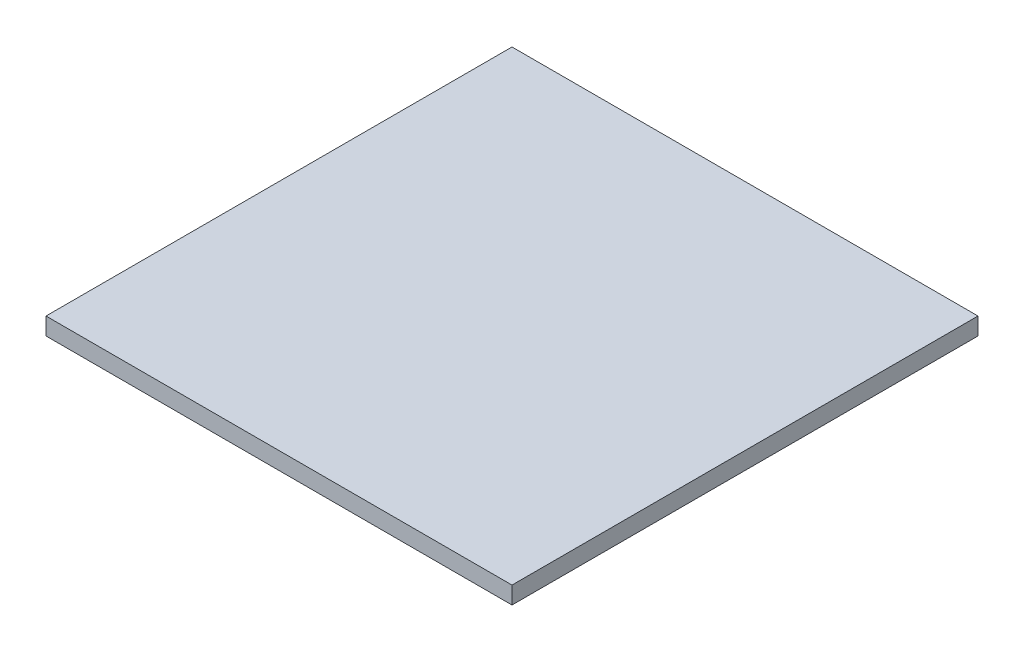
SolidWorks part; units mm, degrees
material "Plastique personnalisé"
ref_plane "Plan de face" through (0, 0, 0) normal (0, 0, 1) x (1, 0, 0)
ref_plane "Plan de dessus" through (0, 0, 0) normal (0, 1, 0) x (1, 0, 0)
ref_plane "Plan de droite" through (0, 0, 0) normal (1, 0, 0) x (0, 0, -1)
sketch "Esquisse1" plane through (0, 0, 0) normal (0, 1, 0) x (1, 0, 0)
  line L1 (0, 0) -> (7, 0)
  line L2 (0, 0) -> (0, 7)
  line L3 (0, 7) -> (7, 7)
  line L4 (7, 0) -> (7, 7)
  dimension "D1" = 7
  dimension "D2" = 7
extrude "Boss.-Extru.1" add sketch "Esquisse1" along normal blind 0.26
sketch "Esquisse2" plane through (0, 0, 0) normal (0, -1, 0) x (1, 0, 0)
  line L0 (7, -7) -> (6.2, -7) construction
  line L1 (7, -7) -> (0, -7) construction
  line L2 (7, -7) -> (7, -6.2) construction
  line L3 (7, 0) -> (7, -7) construction
  line L4 (0, 0) -> (0, -0.8) construction
  line L5 (0, -7) -> (0, 0) construction
  line L6 (0, 0) -> (0.8, 0) construction
  line L7 (0, 0) -> (7, 0) construction
  line L9 (6.2, -6.2) -> (0.8, -6.2)
  line L10 (6.2, -6.2) -> (6.2, -0.8)
  line L11 (6.2, -0.8) -> (0.8, -0.8)
  line L12 (0.8, -6.2) -> (0.8, -0.8)
  dimension "D1" = 0.8
  dimension "D2" = 0.8
  dimension "D3" = 0.8
  dimension "D4" = 0.8
extrude "Boss.-Extru.2" add sketch "Esquisse2" along normal blind 0.01
sketch "Esquisse5" plane through (0, 0, 0) normal (0, -1, 0) x (1, 0, 0)
  line L0 (7, 0) -> (7, -0.075) construction
  line L1 (7, 0) -> (7, -7) construction
  line L2 (7, -0.075) -> (0, -0.075) construction
  line L3 (0, -7) -> (0, 0) construction
  line L4 (0, 0) -> (0.075, 0) construction
  line L5 (0, 0) -> (7, 0) construction
  line L6 (0.075, 0) -> (0.075, -7) construction
  line L7 (7, -7) -> (0, -7) construction
  line L8 (0, -7) -> (0, -6.925) construction
  line L9 (0, -6.925) -> (7, -6.925) construction
  line L10 (7, -7) -> (6.925, -7) construction
  line L11 (6.925, -7) -> (6.925, 0) construction
  line L12 (6.2, -0.8) -> (6.2, 0) construction
  line L13 (6.2, -6.2) -> (6.2, -7) construction
  line L14 (6.2, -6.2) -> (7, -6.2) construction
  line L15 (6.2, -0.8) -> (7, -0.8) construction
  line L16 (0.8, -6.2) -> (0.8, -7) construction
  line L17 (0.8, -6.2) -> (0, -6.2) construction
  line L18 (0.8, -0.8) -> (0, -0.8) construction
  line L19 (0.8, -0.8) -> (0.8, 0) construction
  line L20 (0.075, -5.9312) -> (0.475, -5.9312)
  line L21 (0.075, -6.1812) -> (0.475, -6.1812)
  line L22 (0.075, -6.1812) -> (0.075, -6.4312)
  line L23 (0.075, -6.4312) -> (0.475, -6.4312)
  line L24 (0.475, -6.1812) -> (0.475, -6.4312)
  line L25 (0.475, -5.6812) -> (0.475, -5.9312)
  line L26 (0.075, -5.6812) -> (0.475, -5.6812)
  line L27 (0.075, -5.6812) -> (0.075, -5.9312)
  line L28 (0.075, 0.5) -> (0.075, -6.5) construction
  line L29 (0.075, -5.4312) -> (0.475, -5.4312)
  line L30 (0.475, -5.1812) -> (0.475, -5.4312)
  line L31 (0.075, -5.1812) -> (0.475, -5.1812)
  line L32 (0.075, -5.1812) -> (0.075, -5.4312)
  line L33 (0.075, 1) -> (0.075, -6) construction
  line L34 (0.075, -4.9312) -> (0.475, -4.9312)
  line L35 (0.475, -4.6812) -> (0.475, -4.9312)
  line L36 (0.075, -4.6812) -> (0.475, -4.6812)
  line L37 (0.075, -4.6812) -> (0.075, -4.9312)
  line L38 (0.075, 1.5) -> (0.075, -5.5) construction
  line L39 (0.075, -4.4312) -> (0.475, -4.4312)
  line L40 (0.475, -4.1812) -> (0.475, -4.4312)
  line L41 (0.075, -4.1812) -> (0.475, -4.1812)
  line L42 (0.075, -4.1812) -> (0.075, -4.4312)
  line L43 (0.075, 2) -> (0.075, -5) construction
  line L44 (0.075, -3.9312) -> (0.475, -3.9312)
  line L45 (0.475, -3.6812) -> (0.475, -3.9312)
  line L46 (0.075, -3.6812) -> (0.475, -3.6812)
  line L47 (0.075, -3.6812) -> (0.075, -3.9312)
  line L48 (0.075, 2.5) -> (0.075, -4.5) construction
  line L49 (0.075, -3.4312) -> (0.475, -3.4312)
  line L50 (0.475, -3.1812) -> (0.475, -3.4312)
  line L51 (0.075, -3.1812) -> (0.475, -3.1812)
  line L52 (0.075, -3.1812) -> (0.075, -3.4312)
  line L53 (0.075, 3) -> (0.075, -4) construction
  line L54 (0.075, -2.9312) -> (0.475, -2.9312)
  line L55 (0.475, -2.6812) -> (0.475, -2.9312)
  line L56 (0.075, -2.6812) -> (0.475, -2.6812)
  line L57 (0.075, -2.6812) -> (0.075, -2.9312)
  line L58 (0.075, 3.5) -> (0.075, -3.5) construction
  line L59 (0.075, -2.4312) -> (0.475, -2.4312)
  line L60 (0.475, -2.1812) -> (0.475, -2.4312)
  line L61 (0.075, -2.1812) -> (0.475, -2.1812)
  line L62 (0.075, -2.1812) -> (0.075, -2.4312)
  line L63 (0.075, 4) -> (0.075, -3) construction
  line L64 (0.075, -1.9312) -> (0.475, -1.9312)
  line L65 (0.475, -1.6812) -> (0.475, -1.9312)
  line L66 (0.075, -1.6812) -> (0.475, -1.6812)
  line L67 (0.075, -1.6812) -> (0.075, -1.9312)
  line L68 (0.075, 4.5) -> (0.075, -2.5) construction
  line L69 (0.075, -1.4312) -> (0.475, -1.4312)
  line L70 (0.475, -1.1812) -> (0.475, -1.4312)
  line L71 (0.075, -1.1812) -> (0.475, -1.1812)
  line L72 (0.075, -1.1812) -> (0.075, -1.4312)
  line L73 (0.075, 5) -> (0.075, -2) construction
  line L74 (0.075, -0.9312) -> (0.475, -0.9312)
  line L75 (0.475, -0.6812) -> (0.475, -0.9312)
  line L76 (0.075, -0.6812) -> (0.475, -0.6812)
  line L77 (0.075, -0.6812) -> (0.075, -0.9312)
  line L78 (0.075, 5.5) -> (0.075, -1.5) construction
  line L79 (3.5, -6.925) -> (3.5, -0.075) construction
  line L80 (6.925, -0.6812) -> (6.925, -0.9312)
  line L81 (6.925, -0.6812) -> (6.525, -0.6812)
  line L82 (6.525, -0.6812) -> (6.525, -0.9312)
  line L83 (6.925, -0.9312) -> (6.525, -0.9312)
  line L84 (6.925, -1.1812) -> (6.925, -1.4312)
  line L85 (6.925, -1.1812) -> (6.525, -1.1812)
  line L86 (6.525, -1.1812) -> (6.525, -1.4312)
  line L87 (6.925, -1.4312) -> (6.525, -1.4312)
  line L88 (6.925, -1.6812) -> (6.925, -1.9312)
  line L89 (6.925, -1.6812) -> (6.525, -1.6812)
  line L90 (6.525, -1.6812) -> (6.525, -1.9312)
  line L91 (6.925, -1.9312) -> (6.525, -1.9312)
  line L92 (6.925, -2.1812) -> (6.925, -2.4312)
  line L93 (6.925, -2.1812) -> (6.525, -2.1812)
  line L94 (6.525, -2.1812) -> (6.525, -2.4312)
  line L95 (6.925, -2.4312) -> (6.525, -2.4312)
  line L96 (6.925, -2.6812) -> (6.925, -2.9312)
  line L97 (6.925, -2.6812) -> (6.525, -2.6812)
  line L98 (6.525, -2.6812) -> (6.525, -2.9312)
  line L99 (6.925, -2.9312) -> (6.525, -2.9312)
  line L100 (6.925, -3.1812) -> (6.925, -3.4312)
  line L101 (6.925, -3.1812) -> (6.525, -3.1812)
  line L102 (6.525, -3.1812) -> (6.525, -3.4312)
  line L103 (6.925, -3.4312) -> (6.525, -3.4312)
  line L104 (6.925, -3.6812) -> (6.925, -3.9312)
  line L105 (6.925, -3.6812) -> (6.525, -3.6812)
  line L106 (6.525, -3.6812) -> (6.525, -3.9312)
  line L107 (6.925, -3.9312) -> (6.525, -3.9312)
  line L108 (6.925, -4.1812) -> (6.925, -4.4312)
  line L109 (6.925, -4.1812) -> (6.525, -4.1812)
  line L110 (6.525, -4.1812) -> (6.525, -4.4312)
  line L111 (6.925, -4.4312) -> (6.525, -4.4312)
  line L112 (6.925, -4.6812) -> (6.925, -4.9312)
  line L113 (6.925, -4.6812) -> (6.525, -4.6812)
  line L114 (6.525, -4.6812) -> (6.525, -4.9312)
  line L115 (6.925, -4.9312) -> (6.525, -4.9312)
  line L116 (6.925, -5.1812) -> (6.925, -5.4312)
  line L117 (6.925, -5.1812) -> (6.525, -5.1812)
  line L118 (6.525, -5.1812) -> (6.525, -5.4312)
  line L119 (6.925, -5.4312) -> (6.525, -5.4312)
  line L120 (6.925, -5.6812) -> (6.925, -5.9312)
  line L121 (6.925, -5.6812) -> (6.525, -5.6812)
  line L122 (6.525, -5.6812) -> (6.525, -5.9312)
  line L123 (6.925, -5.9312) -> (6.525, -5.9312)
  line L124 (6.925, -6.1812) -> (6.925, -6.4312)
  line L125 (6.925, -6.1812) -> (6.525, -6.1812)
  line L126 (6.525, -6.1812) -> (6.525, -6.4312)
  line L127 (6.925, -6.4312) -> (6.525, -6.4312)
  dimension "D1" = 0.25
  dimension "D2" = 0.4
  dimension "D3" = 12
extrude "Boss.-Extru.5" add sketch "Esquisse5" along normal blind 0.01
sketch "Esquisse6" plane through (0, 0, 0) normal (0, -1, 0) x (1, 0, 0)
  line L0 (5.6487, -6.9245) -> (5.8987, -6.9245)
  line L1 (6.1487, -6.9245) -> (6.3987, -6.9245)
  line L2 (6.1487, -6.9245) -> (6.1487, -6.5245)
  line L3 (6.1487, -6.5245) -> (6.3987, -6.5245)
  line L4 (6.3987, -6.9245) -> (6.3987, -6.5245)
  line L5 (5.8987, -6.9245) -> (5.8987, -6.5245)
  line L6 (5.6487, -6.5245) -> (5.8987, -6.5245)
  line L7 (5.6487, -6.9245) -> (5.6487, -6.5245)
  line L8 (5.1487, -6.9245) -> (5.3987, -6.9245)
  line L9 (5.3987, -6.9245) -> (5.3987, -6.5245)
  line L10 (5.1487, -6.5245) -> (5.3987, -6.5245)
  line L11 (5.1487, -6.9245) -> (5.1487, -6.5245)
  line L12 (4.6487, -6.9245) -> (4.8987, -6.9245)
  line L13 (4.8987, -6.9245) -> (4.8987, -6.5245)
  line L14 (4.6487, -6.5245) -> (4.8987, -6.5245)
  line L15 (4.6487, -6.9245) -> (4.6487, -6.5245)
  line L16 (4.1487, -6.9245) -> (4.3987, -6.9245)
  line L17 (4.3987, -6.9245) -> (4.3987, -6.5245)
  line L18 (4.1487, -6.5245) -> (4.3987, -6.5245)
  line L19 (4.1487, -6.9245) -> (4.1487, -6.5245)
  line L20 (3.6487, -6.9245) -> (3.8987, -6.9245)
  line L21 (3.8987, -6.9245) -> (3.8987, -6.5245)
  line L22 (3.6487, -6.5245) -> (3.8987, -6.5245)
  line L23 (3.6487, -6.9245) -> (3.6487, -6.5245)
  line L24 (3.1487, -6.9245) -> (3.3987, -6.9245)
  line L25 (3.3987, -6.9245) -> (3.3987, -6.5245)
  line L26 (3.1487, -6.5245) -> (3.3987, -6.5245)
  line L27 (3.1487, -6.9245) -> (3.1487, -6.5245)
  line L28 (2.6487, -6.9245) -> (2.8987, -6.9245)
  line L29 (2.8987, -6.9245) -> (2.8987, -6.5245)
  line L30 (2.6487, -6.5245) -> (2.8987, -6.5245)
  line L31 (2.6487, -6.9245) -> (2.6487, -6.5245)
  line L32 (2.1487, -6.9245) -> (2.3987, -6.9245)
  line L33 (2.3987, -6.9245) -> (2.3987, -6.5245)
  line L34 (2.1487, -6.5245) -> (2.3987, -6.5245)
  line L35 (2.1487, -6.9245) -> (2.1487, -6.5245)
  line L36 (1.6487, -6.9245) -> (1.8987, -6.9245)
  line L37 (1.8987, -6.9245) -> (1.8987, -6.5245)
  line L38 (1.6487, -6.5245) -> (1.8987, -6.5245)
  line L39 (1.6487, -6.9245) -> (1.6487, -6.5245)
  line L40 (1.1487, -6.9245) -> (1.3987, -6.9245)
  line L41 (1.3987, -6.9245) -> (1.3987, -6.5245)
  line L42 (1.1487, -6.5245) -> (1.3987, -6.5245)
  line L43 (1.1487, -6.9245) -> (1.1487, -6.5245)
  line L44 (0.6487, -6.9245) -> (0.8987, -6.9245)
  line L45 (0.8987, -6.9245) -> (0.8987, -6.5245)
  line L46 (0.6487, -6.5245) -> (0.8987, -6.5245)
  line L47 (0.6487, -6.9245) -> (0.6487, -6.5245)
  line L48 (7, 0) -> (7, -7) construction
  line L49 (7, -3.5) -> (0, -3.5) construction
  line L50 (0, -7) -> (0, 0) construction
  line L51 (2.3987, -0.0755) -> (2.3987, -0.4755)
  line L52 (0.6487, -0.4755) -> (0.8987, -0.4755)
  line L53 (0.6487, -0.0755) -> (0.6487, -0.4755)
  line L54 (0.6487, -0.0755) -> (0.8987, -0.0755)
  line L55 (0.8987, -0.0755) -> (0.8987, -0.4755)
  line L56 (1.3987, -0.0755) -> (1.3987, -0.4755)
  line L57 (1.1487, -0.0755) -> (1.3987, -0.0755)
  line L58 (1.1487, -0.0755) -> (1.1487, -0.4755)
  line L59 (1.1487, -0.4755) -> (1.3987, -0.4755)
  line L60 (1.6487, -0.4755) -> (1.8987, -0.4755)
  line L61 (1.6487, -0.0755) -> (1.6487, -0.4755)
  line L62 (1.6487, -0.0755) -> (1.8987, -0.0755)
  line L63 (1.8987, -0.0755) -> (1.8987, -0.4755)
  line L64 (2.1487, -0.4755) -> (2.3987, -0.4755)
  line L65 (2.1487, -0.0755) -> (2.1487, -0.4755)
  line L66 (2.1487, -0.0755) -> (2.3987, -0.0755)
  line L67 (2.6487, -0.0755) -> (2.6487, -0.4755)
  line L68 (2.6487, -0.4755) -> (2.8987, -0.4755)
  line L69 (2.8987, -0.0755) -> (2.8987, -0.4755)
  line L70 (2.6487, -0.0755) -> (2.8987, -0.0755)
  line L71 (3.3987, -0.0755) -> (3.3987, -0.4755)
  line L72 (3.1487, -0.0755) -> (3.3987, -0.0755)
  line L73 (3.1487, -0.0755) -> (3.1487, -0.4755)
  line L74 (3.1487, -0.4755) -> (3.3987, -0.4755)
  line L75 (3.6487, -0.4755) -> (3.8987, -0.4755)
  line L76 (3.6487, -0.0755) -> (3.6487, -0.4755)
  line L77 (3.6487, -0.0755) -> (3.8987, -0.0755)
  line L78 (3.8987, -0.0755) -> (3.8987, -0.4755)
  line L79 (4.1487, -0.0755) -> (4.1487, -0.4755)
  line L80 (4.1487, -0.4755) -> (4.3987, -0.4755)
  line L81 (4.1487, -0.0755) -> (4.3987, -0.0755)
  line L82 (4.3987, -0.0755) -> (4.3987, -0.4755)
  line L83 (4.6487, -0.0755) -> (4.6487, -0.4755)
  line L84 (4.6487, -0.0755) -> (4.8987, -0.0755)
  line L85 (4.8987, -0.0755) -> (4.8987, -0.4755)
  line L86 (4.6487, -0.4755) -> (4.8987, -0.4755)
  line L87 (5.1487, -0.4755) -> (5.3987, -0.4755)
  line L88 (5.1487, -0.0755) -> (5.1487, -0.4755)
  line L89 (5.1487, -0.0755) -> (5.3987, -0.0755)
  line L90 (5.3987, -0.0755) -> (5.3987, -0.4755)
  line L91 (5.6487, -0.0755) -> (5.6487, -0.4755)
  line L92 (5.6487, -0.4755) -> (5.8987, -0.4755)
  line L93 (5.8987, -0.0755) -> (5.8987, -0.4755)
  line L94 (5.6487, -0.0755) -> (5.8987, -0.0755)
  line L95 (6.1487, -0.0755) -> (6.3987, -0.0755)
  line L96 (6.1487, -0.0755) -> (6.1487, -0.4755)
  line L97 (6.1487, -0.4755) -> (6.3987, -0.4755)
  line L98 (6.3987, -0.0755) -> (6.3987, -0.4755)
  dimension "D1" = 0.4
  dimension "D2" = 0.25
  dimension "D3" = 12
sketch "Esquisse7" plane through (0, 0, 0) normal (0, -1, 0) x (1, 0, 0)
  line L0 (7, -3.5) -> (0, -3.5) construction
  line L1 (7, 0) -> (7, -7) construction
  line L2 (0, -7) -> (0, 0) construction
extrude "Boss.-Extru.6" add sketch "Esquisse6" along normal blind 0.01
sketch "Esquisse8" plane through (0, -0.01, 0) normal (0, -1, 0) x (1, 0, 0)
  line L0 (0.8, -6.2) -> (1.05, -6.2)
  line L1 (0.8, -6.2) -> (6.2, -6.2) construction
  line L2 (0.8, -6.2) -> (0.8, -5.954)
  line L3 (0.8, -0.8) -> (0.8, -6.2) construction
  line L4 (1.05, -6.2) -> (0.8, -5.954)
  dimension "D1" = 0.25
  dimension "D2" = 0.246
extrude "Enlèv. mat.-Extru.1" cut sketch "Esquisse8" against normal blind 0.01
